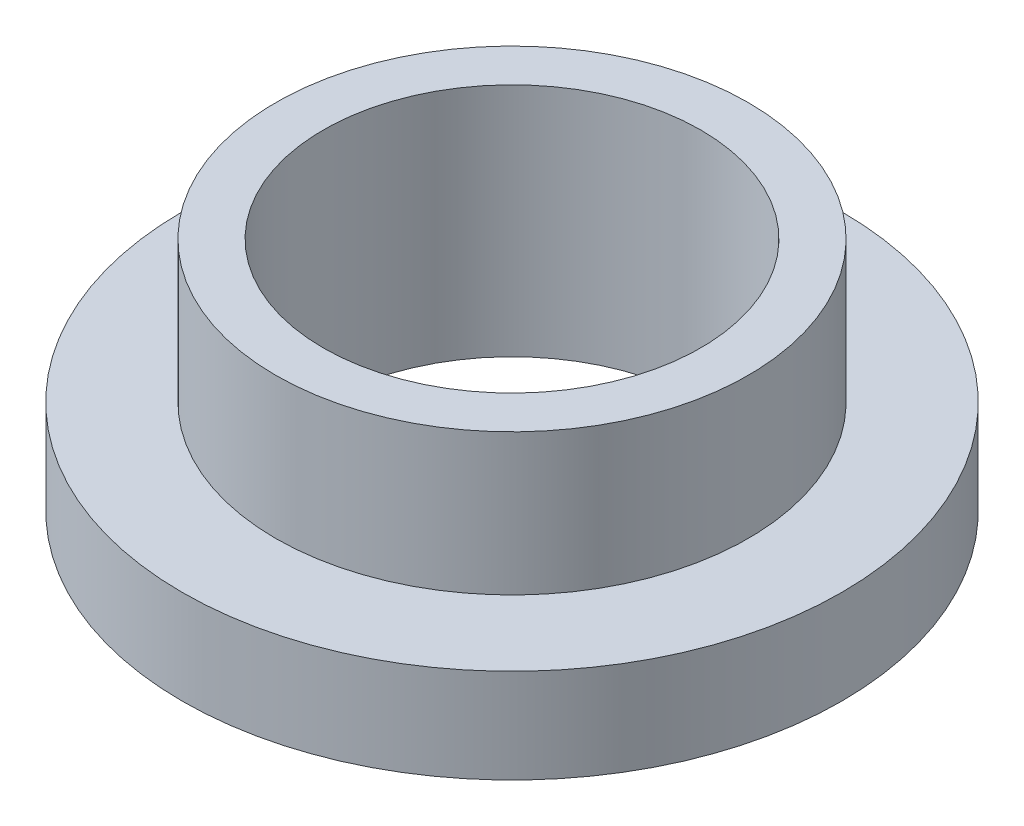
SolidWorks part; units mm, degrees
material "Phosphor bronze 10% D, UNS C52400"
ref_plane "Front" through (0, 0, 0) normal (0, 0, 1) x (1, 0, 0)
ref_plane "Top" through (0, 0, 0) normal (0, 1, 0) x (1, 0, 0)
ref_plane "Right" through (0, 0, 0) normal (1, 0, 0) x (0, 0, -1)
sketch "Sketch1" plane through (0, 0, 0) normal (0, 1, 0) x (1, 0, 0)
  circle A0 centre (0, 0) radius 6.3627
  circle A1 centre (0, 0) radius 7.9629
  circle A2 centre (0, 0) radius 11.1125
  dimension "ID" = 12.7254
  dimension "OD" = 15.9258
  dimension "FlangeOD" = 22.225
sketch "Sketch2" plane through (0, 0, 0) normal (0, 1, 0) x (1, 0, 0)
  circle A0 centre (0, 0) radius 6.3627 construction
  circle A1 centre (0, 0) radius 7.9629 construction
  circle A2 centre (0, 0) radius 6.3627
  circle A3 centre (0, 0) radius 7.9629
extrude "Boss-Extrude1" add sketch "Sketch2" along normal blind 7.9375
sketch "Sketch3" plane through (0, 0, 0) normal (0, 1, 0) x (1, 0, 0)
  circle A0 centre (0, 0) radius 11.1125 construction
  circle A1 centre (0, 0) radius 7.9629 construction
  circle A2 centre (0, 0) radius 11.1125
  circle A3 centre (0, 0) radius 7.9629
extrude "Boss-Extrude2" add sketch "Sketch3" along normal blind 3.175
